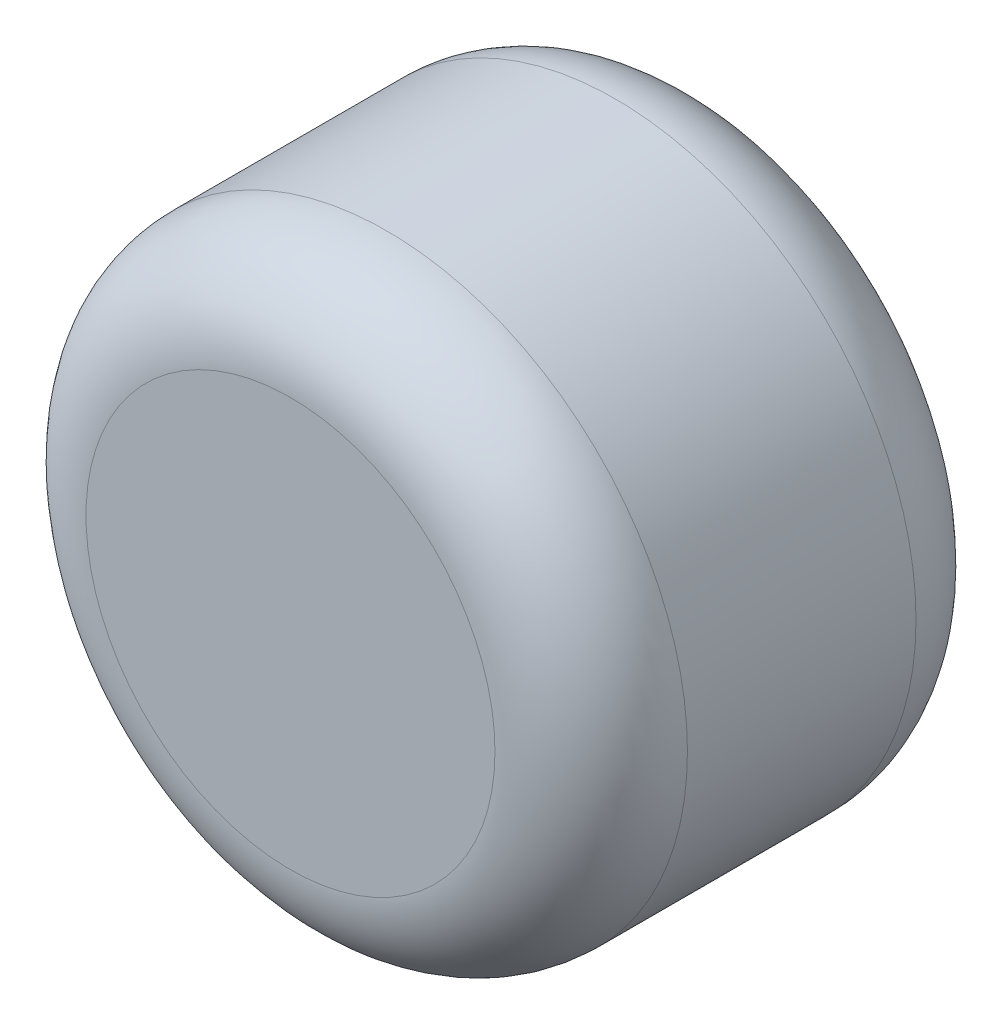
SolidWorks part; units mm, degrees
ref_plane "Front Plane" through (0, 0, 0) normal (0, 0, 1) x (1, 0, 0)
ref_plane "Top Plane" through (0, 0, 0) normal (0, 1, 0) x (1, 0, 0)
ref_plane "Right Plane" through (0, 0, 0) normal (1, 0, 0) x (0, 0, -1)
sketch "Sketch1" plane through (0, 0, 0) normal (0, 0, 1) x (1, 0, 0)
  circle A0 centre (0, 0) radius 63.5
  dimension "D1" = 127
extrude "Boss-Extrude1" add sketch "Sketch1" along normal mid plane 88.9
fillet "Fillet1" radius 20.32 2 edges at (63.5, 0, -44.45) (63.5, 0, 44.45)
